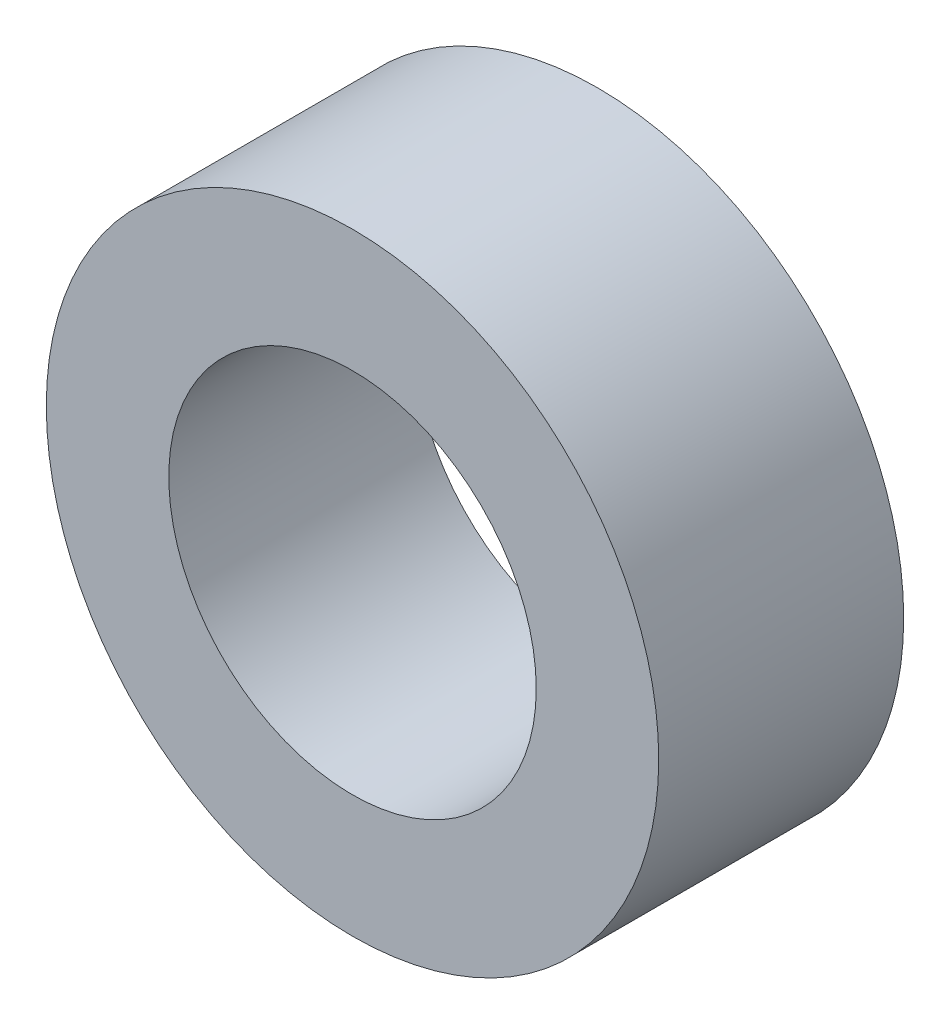
SolidWorks part; units mm, degrees
material "Aluminum Bronze"
ref_plane "Front Plane" through (0, 0, 0) normal (0, 0, 1) x (1, 0, 0)
ref_plane "Top Plane" through (0, 0, 0) normal (0, 1, 0) x (1, 0, 0)
ref_plane "Right Plane" through (0, 0, 0) normal (1, 0, 0) x (0, 0, -1)
sketch "Sketch1" plane through (0, 0, 0) normal (0, 0, 1) x (1, 0, 0)
  circle A0 centre (0, 0) radius 4.7625
  circle A1 centre (0, 0) radius 7.9375
  dimension "D1" = 9.525
  dimension "D2" = 15.875
extrude "Boss-Extrude1" add sketch "Sketch1" along normal blind 6.35
